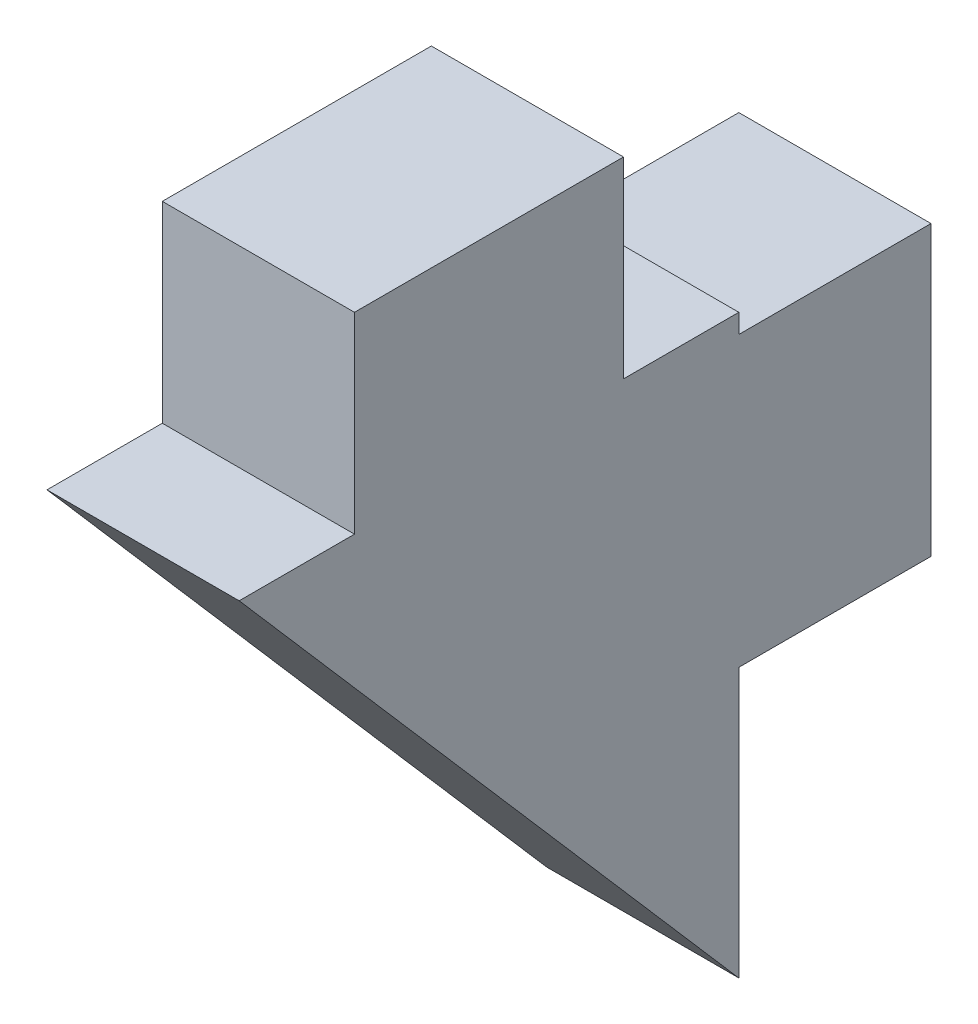
SolidWorks part; units mm, degrees
material "Balsa"
ref_plane "Alzado" through (0, 0, 0) normal (0, 0, 1) x (1, 0, 0)
ref_plane "Planta" through (0, 0, 0) normal (0, 1, 0) x (1, 0, 0)
ref_plane "Vista lateral" through (0, 0, 0) normal (1, 0, 0) x (0, 0, -1)
sketch "Croquis1" plane through (0, 0, 0) normal (1, 0, 0) x (0, 0, -1)
  line L1 (0, 31.6914) -> (-3, 31.6914)
  line L2 (-13, 31.6914) -> (0, 16.6914)
  line L3 (-10, 31.6914) -> (-13, 31.6914)
  line L9 (-3, 31.6914) -> (-3, 36.6914)
  line L10 (-3, 36.6914) -> (-10, 36.6914)
  line L11 (-10, 31.6914) -> (-10, 36.6914)
  line L18 (0, 23.6914) -> (5, 23.6914)
  line L20 (5, 31.1914) -> (5, 23.6914)
  line L21 (0, 23.6914) -> (0, 16.6914)
  line L22 (0, 31.1914) -> (0, 31.6914)
  line L23 (0, 31.1914) -> (5, 31.1914)
  dimension "D1" = 15
  dimension "D2" = 13
  dimension "D3" = 5
  dimension "D4" = 7.5
  dimension "D5" = 7
  dimension "D6" = 0.5
  dimension "D7" = 5
extrude "Saliente-Extruir2" add sketch "Croquis1" along normal blind 5
